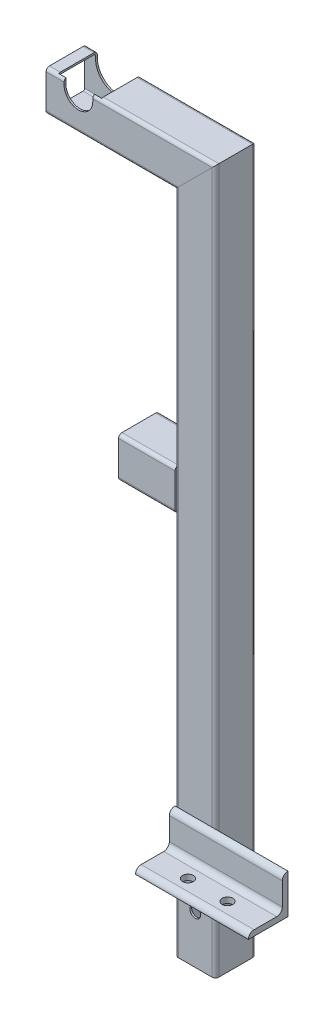
SolidWorks part; units mm, degrees
ref_plane "Front Plane" through (0, 0, 0) normal (0, 0, 1) x (1, 0, 0)
ref_plane "Top Plane" through (0, 0, 0) normal (0, 1, 0) x (1, 0, 0)
ref_plane "Right Plane" through (0, 0, 0) normal (1, 0, 0) x (0, 0, -1)
sketch "Sketch1" plane through (0, 0, 0) normal (0, 0, 1) x (1, 0, 0)
  line L0 (361.4375, 0) -> (361.4375, 526)
  line L1 (361.4375, 526) -> (229.3375, 526)
  line L2 (361.4375, 0) -> (361.4375, -80)
  line L3 (343.5375, 157.0549) -> (343.5375, -80) construction
  line L4 (348.3, 157.0549) -> (348.3, -80) construction
  line L5 (361.4375, 157.0549) -> (361.4375, -80) construction
  line L6 (361.4375, 276.9) -> (293.5375, 276.9)
  dimension "D1" = 526
  dimension "D2" = 80
  dimension "D3" = 132.1
  dimension "D4" = 4.7625
  dimension "D5" = 17.9
  dimension "D6" = 348.3
  dimension "D7" = 276.9
  dimension "D8" = 67.9
other "Structural MemberMain"
ref_plane "Plane1" through (361.4375, 0, 0) normal (0, 1, 0) x (-1, 0, 0)
sketch "Sketch11" plane through (361.4375, 0, 0) normal (0, 1, 0) x (-1, 0, 0)
  line L0 (-14.9, 16.3) -> (14.9, 16.3)
  line L1 (-14.9, 17.9) -> (14.9, 17.9)
  line L2 (-17.9, 14.9) -> (-17.9, -14.9)
  line L3 (-14.9, -17.9) -> (14.9, -17.9)
  line L4 (17.9, 14.9) -> (17.9, -14.9)
  line L5 (-17.9, 17.9) -> (17.9, -17.9) construction
  line L6 (-17.9, -17.9) -> (17.9, 17.9) construction
  line L7 (16.3, 14.9) -> (16.3, -14.9)
  line L8 (-14.9, -16.3) -> (14.9, -16.3)
  line L9 (-16.3, 14.9) -> (-16.3, -14.9)
  arc A0 (-17.9, -14.9) -> (-14.9, -17.9) centre (-14.9, -14.9) ccw
  arc A1 (14.9, -17.9) -> (17.9, -14.9) centre (14.9, -14.9) ccw
  arc A2 (17.9, 14.9) -> (14.9, 17.9) centre (14.9, 14.9) ccw
  arc A3 (-14.9, 17.9) -> (-17.9, 14.9) centre (-14.9, 14.9) ccw
  arc A4 (16.3, 14.9) -> (14.9, 16.3) centre (14.9, 14.9) ccw
  arc A5 (14.9, -16.3) -> (16.3, -14.9) centre (14.9, -14.9) ccw
  arc A6 (-16.3, -14.9) -> (-14.9, -16.3) centre (-14.9, -14.9) ccw
  arc A7 (-14.9, 16.3) -> (-16.3, 14.9) centre (-14.9, 14.9) ccw
  point P0 (0, 0)
  point P30 (0, 0)
  dimension "D3" = 3
  dimension "D1" = 35.8
  dimension "D2" = 35.8
  dimension "D4" = 1.6
sketch "Sketch12" plane through (0, 0, 0) normal (0, 0, 1) x (1, 0, 0)
  line L1 (258, 538.7) -> (258, 549.1) construction
  line L2 (245.3, 538.7) -> (245.3, 549.1)
  line L3 (270.7, 538.7) -> (270.7, 549.1)
  line L4 (361.4375, 526) -> (229.3375, 526) construction
  line L5 (229.3375, 543.9) -> (379.3375, 543.9) construction
  arc A0 (245.3, 538.7) -> (270.7, 538.7) centre (258, 538.7) ccw
  arc A1 (270.7, 549.1) -> (245.3, 549.1) centre (258, 549.1) ccw
  point P2 (258, 543.9)
  dimension "D1" = 25.4
  dimension "D2" = 258
extrude "Cut-ExtrudeTopRailGuide" cut sketch "Sketch12" against normal through all and the other way through all
sketch "Sketch13" plane through (0, 0, 0) normal (0, 1, 0) x (1, 0, 0)
  line L0 (343.5375, -17.9) -> (443.5375, -17.9)
  line L1 (270.7, -17.9) -> (376.3375, -17.9) construction
  line L2 (343.5375, -14.9) -> (343.5375, 14.9) construction
  point P4 (393.5375, -17.9)
  dimension "D1" = 100
other "Structural MemberAngle"
ref_plane "Plane2" through (343.5375, 0, 17.9) normal (1, 0, 0) x (0, 1, 0)
sketch "Sketch14" plane through (343.5375, 0, 17.9) normal (1, 0, 0) x (0, 1, 0)
  line L0 (0, 0) -> (0, 35)
  line L1 (0, 17.5) -> (5, 17.5) construction
  line L2 (5, 30) -> (5, 10)
  line L3 (10, 5) -> (30, 5)
  line L4 (17.5, 5) -> (17.5, 0) construction
  line L5 (35, 0) -> (0, 0)
  arc A0 (35, 0) -> (30, 5) centre (30, 0) ccw
  arc A1 (0, 35) -> (5, 30) centre (0, 30) cw
  arc A2 (10, 5) -> (5, 10) centre (10, 10) cw
  point P10 (17.5, 0)
  point P14 (0, 17.5)
  point P15 (5, 17.5)
  point P16 (17.5, 5)
  point P17 (5, 35)
  point P18 (35, 5)
  point P21 (0, 0)
  dimension "D2" = 5
  dimension "D3" = 35
  dimension "Radius_1" = 5
  dimension "D1" = 5
sketch "Sketch15" plane through (0, 0, 0) normal (0, 1, 0) x (1, 0, 0)
  line L0 (393.5375, -17.9) -> (393.5375, -52.9) construction
  line L1 (443.5375, -52.9) -> (343.5375, -52.9) construction
  line L2 (-65.8005, -37.9) -> (852.8755, -37.9) construction
  line L3 (343.5375, -17.9) -> (443.5375, -17.9) construction
  line L4 (0, 28.933) -> (0, -28.933) construction
  circle A0 centre (312.8, -37.9) radius 4.7625 construction
  circle A1 centre (348.3, -37.9) radius 5.0441 construction
  circle A2 centre (375, -37.9) radius 4.7625
  circle A3 centre (410, -37.9) radius 4.7625
  point P7 (393.5375, -37.9)
  point P16 (0, 0)
  dimension "D2" = 9.525
  dimension "D1" = 20
  dimension "D3" = 348.3
  dimension "D4" = 35.5
  dimension "D5" = 35
  dimension "D6" = 410
extrude "Cut-ExtrudeMountingHoles" cut sketch "Sketch15" along normal through all
sketch "Sketch16" plane through (0, 0, 0) normal (0, 0, 1) x (1, 0, 0)
  line L4 (277.05, 538.7) -> (277.05, 549.1)
  line L5 (238.95, 549.1) -> (238.95, 538.7)
  line L6 (277.05, 538.7) -> (277.05, 549.1)
  line L7 (238.95, 549.1) -> (238.95, 538.7)
  arc A4 (238.95, 538.7) -> (277.05, 538.7) centre (258, 538.7) ccw
  arc A5 (277.05, 549.1) -> (238.95, 549.1) centre (258, 549.1) ccw
  arc A6 (238.95, 538.7) -> (277.05, 538.7) centre (258, 538.7) ccw
  arc A7 (277.05, 549.1) -> (238.95, 549.1) centre (258, 549.1) ccw
  dimension "D1" = 6.35
extrude "Cut-ExtrudeEnlargeRailGuide" cut sketch "Sketch16" against normal through all and the other way up to surface other way up to face at (276.6938, 531.3125, 16.3)
sketch "Sketch17" plane through (0, 0, 0) normal (0, 0, 1) x (1, 0, 0)
  line L0 (327.7, 289.6) -> (327.7, 300) construction
  line L1 (315, 289.6) -> (315, 300)
  line L2 (340.4, 289.6) -> (340.4, 300)
  line L3 (361.4375, 276.9) -> (293.5375, 276.9) construction
  line L4 (293.5375, 294.8) -> (343.5375, 294.8) construction
  arc A0 (315, 289.6) -> (340.4, 289.6) centre (327.7, 289.6) ccw
  arc A1 (340.4, 300) -> (315, 300) centre (327.7, 300) ccw
  point P2 (327.7, 294.8)
  dimension "D1" = 25.4
  dimension "D2" = 12.7
  dimension "D3" = 327.7
sketch "Sketch18" plane through (0, 0, -17.9) normal (0, 0, -1) x (-1, 0, 0)
  line L0 (-327.7, 276.9) -> (-320.4, 276.9)
  line L1 (-361.4375, 276.9) -> (-293.5375, 276.9) construction
  line L2 (-307.7, 289.6) -> (-307.7, 300)
  line L3 (-327.7, 276.9) -> (-327.7, 300)
  line L4 (-327.7, 300) -> (-307.7, 300)
  arc A0 (-340.4, 289.6) -> (-315, 289.6) centre (-327.7, 289.6) ccw construction
  arc A1 (-307.7, 289.6) -> (-320.4, 276.9) centre (-320.4, 289.6) cw
  point P10 (-307.7, 276.9)
  dimension "D2" = 12.7
  dimension "D1" = 20
sketch "Sketch19" plane through (0, 0, 17.9) normal (0, 0, 1) x (1, 0, 0)
  line L0 (361.4375, 0) -> (361.4375, -80) construction
  line L1 (343.5375, 0) -> (443.5375, 0) construction
  line L2 (379.3375, 0) -> (379.3375, -80) construction
  circle A0 centre (361.4375, -37.5) radius 4.7625
  dimension "D1" = 9.525
  dimension "D3" = 17.9
  dimension "D2" = 37.5
extrude "Cut-Extrude1" cut sketch "Sketch19" against normal through all
